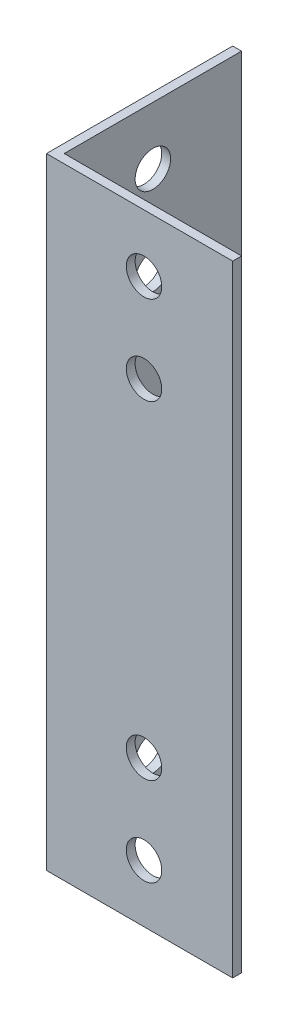
SolidWorks part; units mm, degrees
ref_plane "Face" through (0, 0, 0) normal (0, 0, 1) x (1, 0, 0)
ref_plane "Dessus" through (0, 0, 0) normal (0, 1, 0) x (1, 0, 0)
ref_plane "Droite" through (0, 0, 0) normal (1, 0, 0) x (0, 0, -1)
sketch "Esquisse1" plane through (0, 0, 0) normal (0, 1, 0) x (1, 0, 0)
  line L0 (0, 0) -> (0, 21)
  line L1 (0, 21) -> (1, 21)
  line L2 (1, 21) -> (1, 1)
  line L3 (1, 1) -> (21, 1)
  line L4 (21, 1) -> (21, 0)
  line L5 (21, 0) -> (0, 0)
  dimension "D1" = 1
  dimension "D2" = 1
  dimension "D3" = 90
  dimension "D4" = 20
extrude "Extrusion1" add sketch "Esquisse1" along normal blind 70
sketch "Esquisse2" plane through (1, 0, 0) normal (1, 0, 0) x (0, 0, -1)
  line L0 (1, 35) -> (21, 35) construction
  line L1 (1, 70) -> (1, 0) construction
  line L2 (21, 70) -> (21, 0) construction
  line L3 (11, 0) -> (11, 70) construction
  line L4 (1, 0) -> (21, 0) construction
  line L5 (1, 70) -> (21, 70) construction
  circle A0 centre (11, 16.5) radius 2
  circle A1 centre (11, 6.5) radius 2
  circle A2 centre (11, 53.5) radius 2
  circle A3 centre (11, 63.5) radius 2
  dimension "D1" = 4
  dimension "D2" = 18.5
  dimension "D3" = 10
extrude "Extrusion2" cut sketch "Esquisse2" against normal up to next
sketch "Esquisse3" plane through (0, 0, -1) normal (0, 0, -1) x (-1, 0, 0)
  line L0 (-11, 70) -> (-11, 0) construction
  line L1 (-21, 70) -> (-1, 70) construction
  line L2 (-21, 0) -> (-1, 0) construction
  line L3 (-21, 35) -> (-1, 35) construction
  line L4 (-21, 70) -> (-21, 0) construction
  line L5 (-1, 70) -> (-1, 0) construction
  circle A0 centre (-11, 53.5) radius 2
  circle A1 centre (-11, 63.5) radius 2
  circle A2 centre (-11, 6.5) radius 2
  circle A3 centre (-11, 16.5) radius 2
  dimension "D1" = 4
  dimension "D2" = 18.5
  dimension "D3" = 10
extrude "Extrusion3" cut sketch "Esquisse3" against normal up to next
